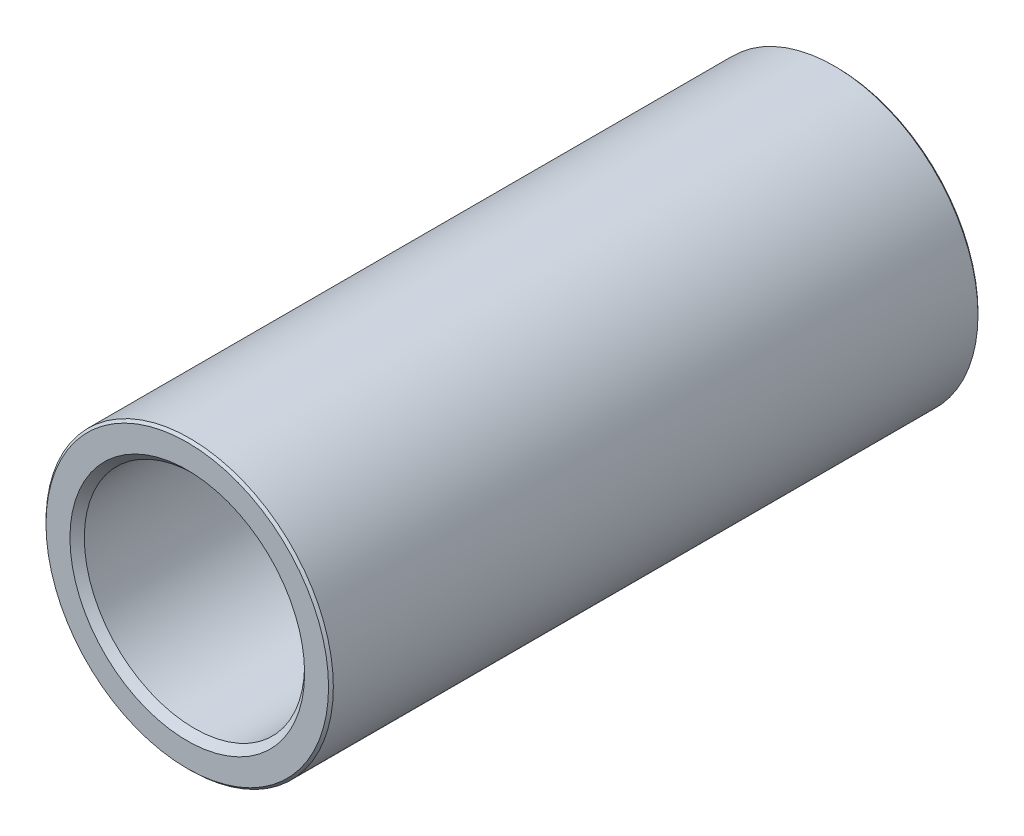
SolidWorks part; units mm, degrees
ref_plane "Front Plane" through (0, 0, 0) normal (0, 0, 1) x (1, 0, 0)
ref_plane "Top Plane" through (0, 0, 0) normal (0, 1, 0) x (1, 0, 0)
ref_plane "Right Plane" through (0, 0, 0) normal (1, 0, 0) x (0, 0, -1)
sketch "Sketch1" plane through (0, 0, 0) normal (0, 0, 1) x (1, 0, 0)
  circle A0 centre (0, 0) radius 15
  circle A1 centre (0, 0) radius 11.5
  dimension "Gudgeon_Pin_Outer_Diameter" = 30
  dimension "D2" = 23
extrude "Boss-Extrude1" add sketch "Sketch1" along normal blind 67.8072
chamfer "Chamfer1" distance 0.25 angle 45 2 edges at (15, 0, 0) (15, 0, 67.8072)
chamfer "Chamfer2" distance 0.75 angle 45 2 edges at (11.5, 0, 67.8072) (11.5, 0, 0)
equation "\"D2@Sketch1\"=\"Gudgeon_Pin_Outer_Diameter@Sketch1\"  - 7"
equation "\"Gudgeon_Pin_Outer_Diameter@Sketch1\"=\"Gudgeon_Diameter@Gudgeon Hole@piston v2-1.Part\""
equation "\"D1@Boss-Extrude1\" = 0.8922 * 2 * \"Piston_Radius@Piston CS@piston v2<1>.Part\""
